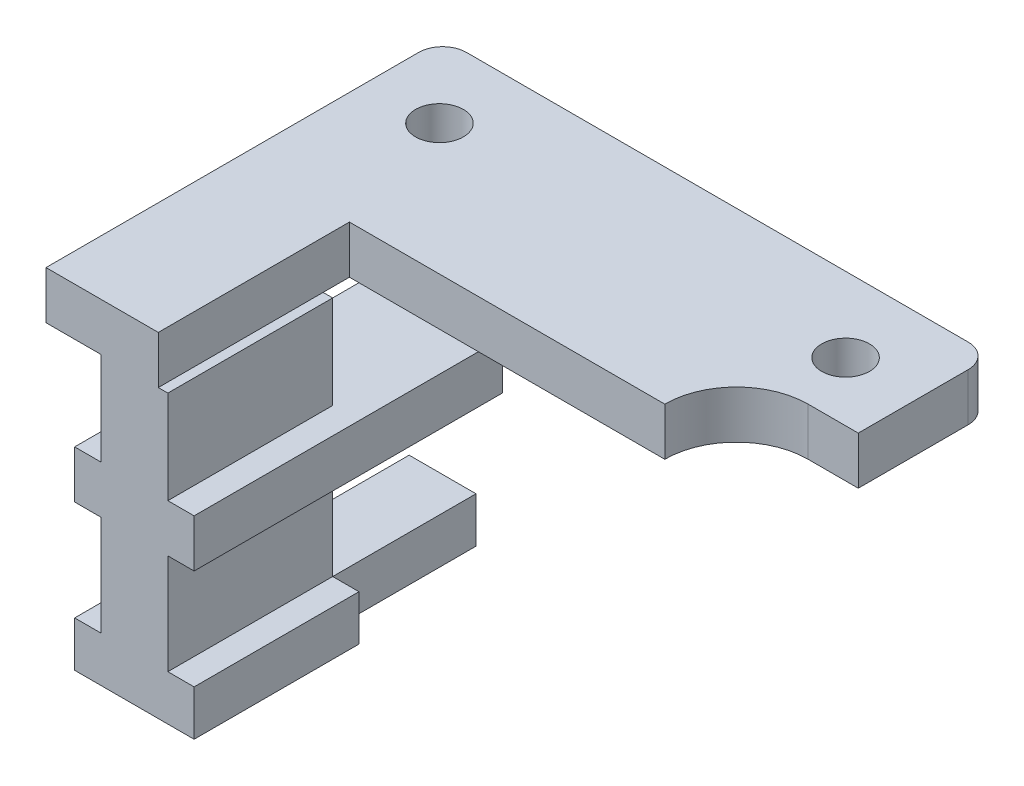
SolidWorks part; units mm, degrees
ref_plane "Front Plane" through (0, 0, 0) normal (0, 0, 1) x (1, 0, 0)
ref_plane "Top Plane" through (0, 0, 0) normal (0, 1, 0) x (1, 0, 0)
ref_plane "Right Plane" through (0, 0, 0) normal (1, 0, 0) x (0, 0, -1)
sketch "Sketch1" plane through (0, 0, 0) normal (0, 1, 0) x (1, 0, 0)
  line L0 (11.7, 3) -> (11.7, 7.6)
  line L1 (10.7, 8.6) -> (-10.3, 8.6)
  line L2 (-11.3, -8) -> (-11.3, 7.6)
  line L5 (11.7, 3) -> (9.6, 3)
  line L6 (-6.6, 0) -> (6.6, 0)
  line L7 (-6.6, 0) -> (-6.6, -8)
  line L8 (-6.6, -8) -> (-11.3, -8)
  arc A0 (9.6, 3) -> (6.6, 0) centre (9.6, 0) ccw
  circle A1 centre (8.7, 5.4696) radius 1
  circle A2 centre (-8.3, 5.4696) radius 1
  arc A3 (-10.3, 8.6) -> (-11.3, 7.6) centre (-10.3, 7.6) ccw
  arc A4 (11.7, 7.6) -> (10.7, 8.6) centre (10.7, 7.6) ccw
  point P0 (0, 0)
  point P8 (0, -3.5)
  dimension "D3" = 3
  dimension "D4" = 2
  dimension "D6" = 1
  dimension "D12" = 3.1304
  dimension "D13" = 3
  dimension "D5" = 17
  dimension "D7" = 13.2
  dimension "D8" = 16.6
  dimension "D9" = 23
  dimension "D10" = 8
  dimension "D11" = 4.7
extrude "Boss-Extrude1" add sketch "Sketch1" along normal blind 2
sketch "Sketch2" plane through (0, 0, 0) normal (0, 0, 1) x (1, 0, 0)
  line L11 (-11.3, 1) -> (-8.7761, 1) construction
  line L12 (-11.3, 2) -> (-11.3, 0) construction
  line L34 (-11.3, 2) -> (-11.3, 0) construction
  line L35 (10.7, 0) -> (-10.3, 0) construction
  line L36 (-9, -10.1) -> (-9, 0)
  line L37 (-9, 0) -> (-6.2, 0)
  line L38 (-6.2, -10.1) -> (-6.2, 0)
  line L39 (-9, -10.1) -> (-10.1, -10.1)
  line L40 (-10.1, -10.1) -> (-10.1, -12)
  line L41 (-10.1, -12) -> (-5.1, -12)
  line L42 (-5.1, -12) -> (-5.1, -10.1)
  line L43 (-5.1, -10.1) -> (-6.2, -10.1)
  point P0 (-8.4, 8)
  dimension "D1" = 2.8
  dimension "D2" = 2.3
  dimension "D3" = 5
  dimension "D4" = 1.9
  dimension "D5" = 10.1
extrude "Boss-Extrude2" add sketch "Sketch2" against normal blind 6.9 from surface at 8 starting at face at (-8.95, 1, 8)
sketch "Sketch3" plane through (0, 0, 8) normal (0, 0, 1) x (1, 0, 0)
  line L0 (-10.1, -12) -> (-5.1, -12) construction
  line L1 (-9, -10.1) -> (-6.2, -10.1)
  line L2 (-9, -10.1) -> (-9, -12)
  line L3 (-9, -12) -> (-6.2, -12)
  line L4 (-6.2, -10.1) -> (-6.2, -12)
  line L5 (-6.2, -10.1) -> (-6.2, 0) construction
  line L6 (-10.1, -10.1) -> (-10.1, -12) construction
  line L7 (-5.1, -5.9) -> (-10.1, -5.9)
  line L8 (-5.1, -5.9) -> (-5.1, -3.9)
  line L9 (-5.1, -3.9) -> (-10.1, -3.9)
  line L10 (-10.1, -5.9) -> (-10.1, -3.9)
  line L11 (-5.1, -5.9) -> (-10.1, -3.9) construction
  line L12 (-5.1, -3.9) -> (-10.1, -5.9) construction
  line L13 (-5.1, -12) -> (-5.1, -10.1) construction
  point P9 (-7.6, -4.9)
  dimension "D1" = 2
  dimension "D2" = 4.2
extrude "Boss-Extrude3" add sketch "Sketch3" against normal blind 12.9
